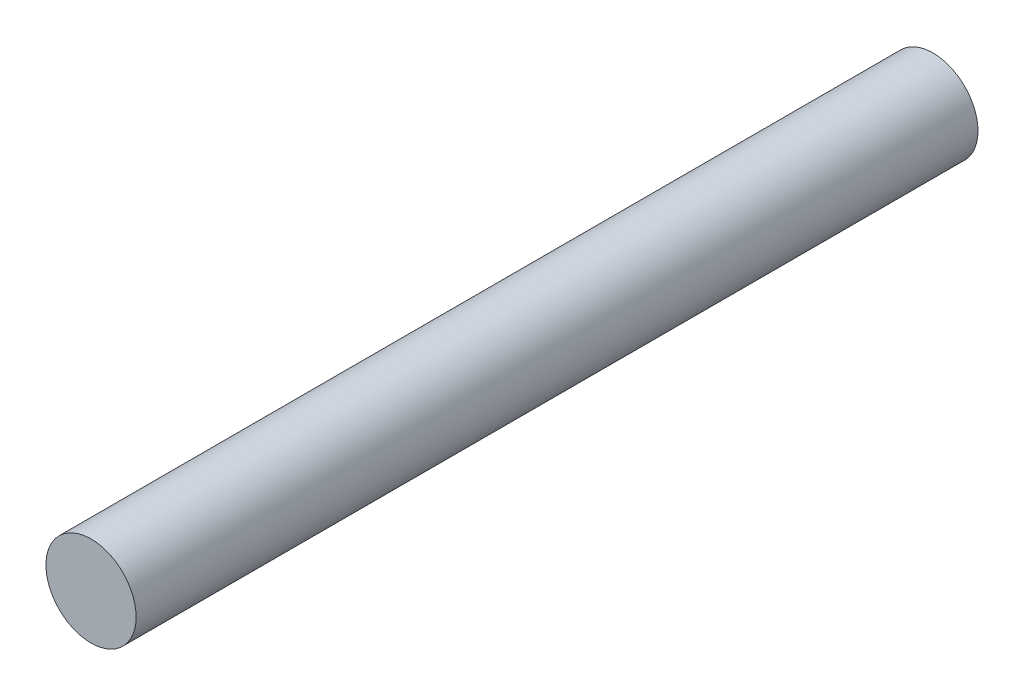
SolidWorks part; units mm, degrees
ref_plane "Front Plane" through (0, 0, 0) normal (0, 0, 1) x (1, 0, 0)
ref_plane "Top Plane" through (0, 0, 0) normal (0, 1, 0) x (1, 0, 0)
ref_plane "Right Plane" through (0, 0, 0) normal (1, 0, 0) x (0, 0, -1)
sketch "Sketch1" plane through (0, 0, 0) normal (0, 0, 1) x (1, 0, 0)
  circle A0 centre (0, 0) radius 0.75
  dimension "D1" = 1.5
extrude "Boss-Extrude1" add sketch "Sketch1" along normal mid plane 14
